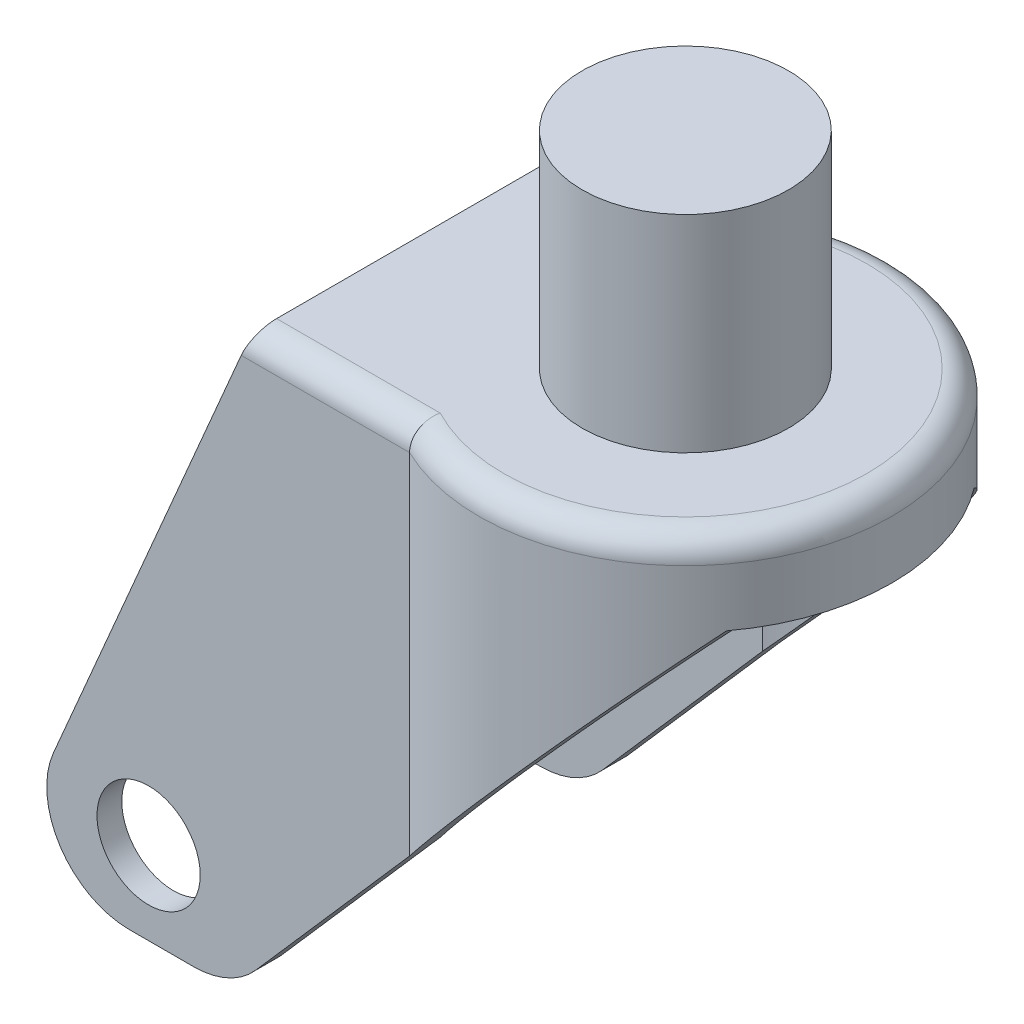
SolidWorks part; units mm, degrees
ref_plane "Front Plane" through (0, 0, 0) normal (0, 0, 1) x (1, 0, 0)
ref_plane "Top Plane" through (0, 0, 0) normal (0, 1, 0) x (1, 0, 0)
ref_plane "Right Plane" through (0, 0, 0) normal (1, 0, 0) x (0, 0, -1)
sketch "Sketch2" plane through (0, 0, 0) normal (0, 1, 0) x (1, 0, 0)
  circle A0 centre (0, 0) radius 25
  dimension "D1" = 50
extrude "Extrude-Thin1" add sketch "Sketch2" against normal blind 60 thin thin type one direction reverse wall 3
sketch "Sketch3" plane through (0, 0, 0) normal (1, 0, 0) x (0, 0, -1)
  line L0 (25, 0) -> (-25, 0) construction
  line L1 (22.5, 0) -> (-22.5, 0)
  line L2 (22.5, 0) -> (22.5, -70)
  line L3 (22.5, -70) -> (-22.5, -70)
  line L4 (-22.5, 0) -> (-22.5, -70)
  line L5 (22.5, 0) -> (-22.5, -70) construction
  line L6 (22.5, -70) -> (-22.5, 0) construction
  point P0 (0, -35)
  dimension "D1" = 70
  dimension "D2" = 45
extrude "Extrude-Thin2" add sketch "Sketch3" against normal blind 60 thin thin type one direction reverse wall 3
sketch "Sketch4" plane through (0, 0, 0) normal (0, 1, 0) x (1, 0, 0)
  circle A0 centre (0, 0) radius 22
extrude "Cut-Extrude1" cut sketch "Sketch4" against normal through all
sketch "Sketch5" plane through (0, 0, 0) normal (0, 0, 1) x (1, 0, 0)
  line L0 (20, -10) -> (-50, -90)
  line L2 (-50, -90) -> (25, -90)
  line L4 (20, -10) -> (25, -10)
  line L6 (25, -10) -> (25, -90)
  dimension "D1" = 75
  dimension "D2" = 10
  dimension "D3" = 25
  dimension "D4" = 80
  dimension "D5" = 5
extrude "Cut-Extrude2" cut sketch "Sketch5" against normal through all both and the other way through all
sketch "Sketch6" plane through (-60, 0, 0) normal (-1, 0, 0) x (0, 0, 1)
  line L0 (19.5, -3) -> (19.5, -67) construction
  line L1 (19.5, -67) -> (-19.5, -67) construction
  line L2 (-19.5, -67) -> (-19.5, -3) construction
  line L3 (-19.5, -3) -> (19.5, -3) construction
  line L4 (19.5, -3) -> (19.5, -67)
  line L5 (19.5, -67) -> (-19.5, -67)
  line L6 (-19.5, -67) -> (-19.5, -3)
  line L7 (-19.5, -3) -> (19.5, -3)
extrude "Cut-Extrude3" cut sketch "Sketch6" against normal blind 50
sketch "Sketch7" plane through (0, 0, 0) normal (0, 0, 1) x (1, 0, 0)
  line L0 (-30, 0) -> (-60, -70)
  line L1 (-60, 0) -> (-10.8972, 0) construction
  line L2 (-30, 0) -> (-60, 0)
  line L3 (-60, 0) -> (-60, -70)
  dimension "D1" = 30
extrude "Cut-Extrude4" cut sketch "Sketch7" against normal through all both and the other way through all
sketch "Sketch8" plane through (0, -67, 0) normal (0, 1, 0) x (1, 0, 0)
  line L3 (-58.7143, 19.5) -> (-58.7143, -19.5)
  line L4 (-29.875, 19.5) -> (-58.7143, 19.5)
  line L6 (-58.7143, -19.5) -> (-29.875, -19.5)
  line L7 (-29.875, -19.5) -> (-29.875, 19.5)
  line L8 (-29.875, 19.5) -> (-64.875, 19.5)
  line L9 (-64.875, 19.5) -> (-64.875, -19.5)
  line L10 (-64.875, -19.5) -> (-29.875, -19.5)
  line L12 (-29.875, -19.5) -> (-29.875, 19.5)
  dimension "D2" = 35
  dimension "D3" = 39
  dimension "D1" = 0
extrude "Cut-Extrude6" cut sketch "Sketch8" against normal through all
sketch "Sketch9" plane through (0, 0, 0) normal (0, 1, 0) x (1, 0, 0)
  line L0 (-30, 22.5) -> (-10.8972, 22.5) construction
  line L1 (-30, 22.5) -> (-30, -22.5) construction
  line L2 (-30, -22.5) -> (-10.8972, -22.5) construction
  line L3 (-30, 22.5) -> (-10.8972, 22.5)
  line L4 (-30, 22.5) -> (-30, -22.5)
  line L5 (-30, -22.5) -> (-10.8972, -22.5)
  arc A0 (-10.8972, -22.5) -> (-10.8972, 22.5) centre (0, 0) ccw construction
  arc A1 (-10.8972, -22.5) -> (-10.8972, 22.5) centre (0, 0) ccw
extrude "Boss-Extrude1" add sketch "Sketch9" against normal blind 3
fillet "Fillet1" radius 3 3 edges at (-20.4486, 0, -22.5) (25, 0, 0) (-20.4486, 0, 22.5)
sketch "Sketch10" plane through (0, 0, 22.5) normal (0, 0, 1) x (1, 0, 0)
  line L1 (-60, -70) -> (-32.5, -70) construction
  line L2 (-42.5, -70) -> (-42.5, -60) construction
  circle A0 centre (-42.5, -60) radius 6.25
  dimension "D1" = 12.5
  dimension "D2" = 10
  dimension "D3" = 10
extrude "Cut-Extrude7" cut sketch "Sketch10" against normal through all
fillet "Fillet3" radius 10 4 edges at (-32.5, -70, -21) (-32.5, -70, 21) (-60, -70, -21) (-60, -70, 21)
sketch "Sketch11" plane through (0, 0, 0) normal (0, 1, 0) x (1, 0, 0)
  circle A0 centre (0, 0) radius 12.5
  dimension "D1" = 25
extrude "Boss-Extrude2" add sketch "Sketch11" along normal blind 25
